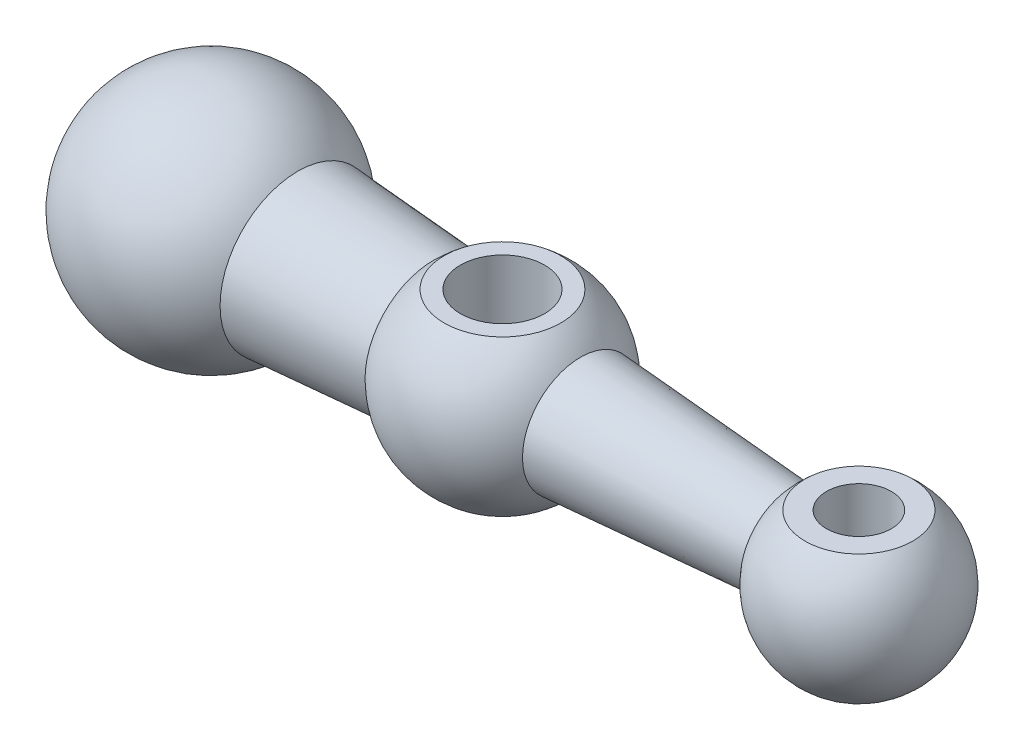
SolidWorks part; units mm, degrees
ref_plane "Front Plane" through (0, 0, 0) normal (0, 0, 1) x (1, 0, 0)
ref_plane "Top Plane" through (0, 0, 0) normal (0, 1, 0) x (1, 0, 0)
ref_plane "Right Plane" through (0, 0, 0) normal (1, 0, 0) x (0, 0, -1)
sketch "Sketch2" plane through (0, 0, 0) normal (0, 0, 1) x (1, 0, 0)
  line L0 (0, 0) -> (120.1579, 0) construction
  line L1 (13.4164, 12) -> (34.3252, 10.5379)
  line L2 (13.4164, 12) -> (25.891, 12) construction
  line L3 (57.0376, 8.9497) -> (88.8737, 6.7235)
  line L4 (0, 0) -> (-36.208, 0) construction
  line L5 (-18, 0) -> (113, 0)
  arc A0 (13.4164, 12) -> (-18, 0) centre (0, 0) ccw
  arc A1 (57.0376, 8.9497) -> (34.3252, 10.5379) centre (45, 0) ccw
  arc A2 (113, 0) -> (88.8737, 6.7235) centre (100, 0) ccw
  point P3 (120.1579, 0)
  dimension "D1" = 36
  dimension "D2" = 30
  dimension "D3" = 26
  dimension "D4" = 45
  dimension "D5" = 100
  dimension "D6" = 12
  dimension "D7" = 4
revolve "Revolve1" add sketch "Sketch2" angle 360 about L5
sketch "Sketch3" plane through (0, 0, 0) normal (0, 1, 0) x (1, 0, 0)
  circle A0 centre (45, 0) radius 6.5
  point P2 (0, 0)
  dimension "D1" = 13
  dimension "D2" = 45
extrude "Cut-Extrude1" cut sketch "Sketch3" against normal through all both and the other way through all
sketch "Sketch4" plane through (0, 0, 0) normal (0, 1, 0) x (1, 0, 0)
  circle A0 centre (100, 0) radius 8.5
  point P2 (0, 0)
  dimension "D1" = 17
  dimension "D2" = 100
extrude "Cut-Extrude2" cut sketch "Sketch4" along normal blind 10 from offset 10
sketch "Sketch5" plane through (0, 10, 0) normal (0, 1, 0) x (1, 0, 0)
  circle A0 centre (100, 0) radius 5
  point P2 (0, 0)
  dimension "D1" = 10
  dimension "D2" = 100
extrude "Cut-Extrude3" cut sketch "Sketch5" against normal blind 10
sketch "Sketch6" plane through (0, 0, 0) normal (0, 1, 0) x (1, 0, 0)
  circle A0 centre (45, 0) radius 9
  dimension "D1" = 18
extrude "Cut-Extrude4" cut sketch "Sketch6" along normal blind 12 from offset 12
mirror "Mirror1" about plane through (0, 0, 0) normal (0, 1, 0) of "Cut-Extrude4"
